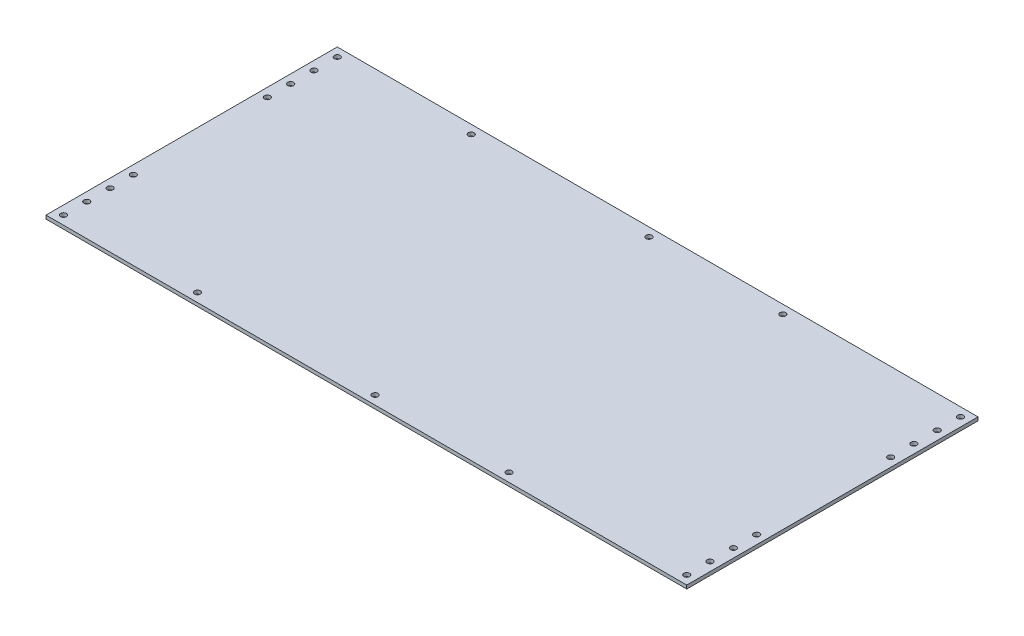
SolidWorks part; units mm, degrees
material "Plain Carbon Steel"
ref_plane "Front Plane" through (0, 0, 0) normal (0, 0, 1) x (1, 0, 0)
ref_plane "Top Plane" through (0, 0, 0) normal (0, 1, 0) x (1, 0, 0)
ref_plane "Right Plane" through (0, 0, 0) normal (1, 0, 0) x (0, 0, -1)
sketch "Sketch1" plane through (0, 0, 0) normal (0, 1, 0) x (1, 0, 0)
  line B0 (-1100, -500) -> (1100, -500)
  line B1 (-1100, -500) -> (-1100, 500)
  line B2 (1100, -500) -> (1100, 500)
  line B3 (-1100, 500) -> (1100, 500)
  circle B4 centre (-1070, 470) radius 10
  circle B5 centre (1070, 470) radius 10
  circle B6 centre (1070, 230) radius 10
  circle B7 centre (1070, 310) radius 10
  circle B8 centre (1070, 390) radius 10
  circle B9 centre (460, 470) radius 10
  circle B10 centre (0, 470) radius 10
  circle B11 centre (-610, 470) radius 10
  circle B12 centre (-1070, 390) radius 10
  circle B13 centre (-1070, 230) radius 10
  circle B14 centre (-1070, 310) radius 10
  circle B15 centre (1070, -230) radius 10
  circle B16 centre (1070, -310) radius 10
  circle B17 centre (1070, -390) radius 10
  circle B18 centre (1070, -470) radius 10
  circle B19 centre (460, -470) radius 10
  circle B20 centre (0, -470) radius 10
  circle B21 centre (-610, -470) radius 10
  circle B22 centre (-1070, -470) radius 10
  circle B23 centre (-1070, -390) radius 10
  circle B24 centre (-1070, -310) radius 10
  circle B25 centre (-1070, -230) radius 10
sketch_block_instance "Bottomplate-1"
sketch_block "Bottomplate" parameters "D6"=20, "D1"=2200, "D2"=1000, "D3"=30, "D4"=30, "D5"=30, "D7"=460, "D8"=610, "D9"=460
extrude "Boss-Extrude1" add sketch "Sketch1" against normal blind 12
